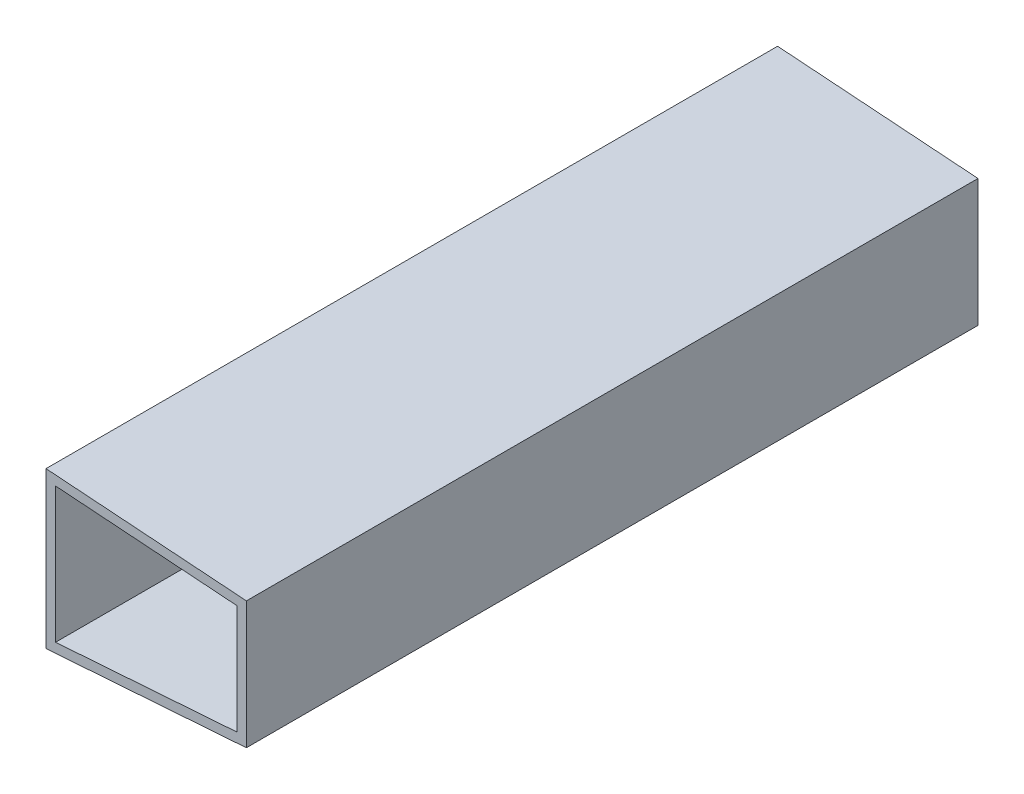
SolidWorks part; units mm, degrees
ref_plane "Front Plane" through (0, 0, 0) normal (0, 0, 1) x (1, 0, 0)
ref_plane "Top Plane" through (0, 0, 0) normal (0, 1, 0) x (1, 0, 0)
ref_plane "Right Plane" through (0, 0, 0) normal (1, 0, 0) x (0, 0, -1)
sketch "Sketch1" plane through (0, 0, 0) normal (0, 0, 1) x (1, 0, 0)
  line L0 (0, -24.5) -> (0, 24.5)
  line L1 (0, 24.5) -> (63, 20)
  line L2 (63, 20) -> (63, -20)
  line L3 (63, -20) -> (0, -24.5)
  point P0 (63, 17.1735)
  point P4 (0, 0)
  point P8 (63, 0)
  dimension "D1" = 49
  dimension "D2" = 40
  dimension "D3" = 63
extrude "Extrude-Thin1" add sketch "Sketch1" along normal blind 230 thin
